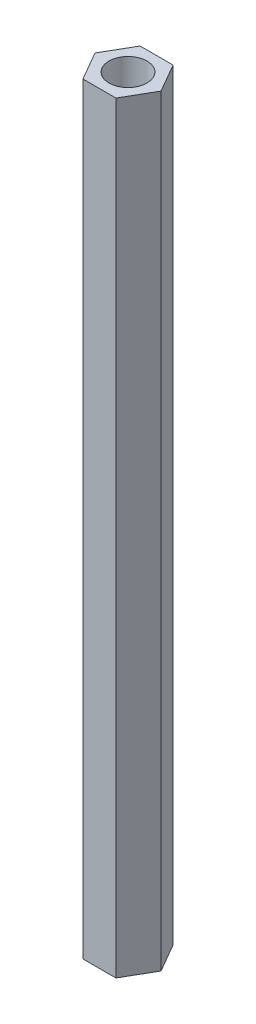
SolidWorks part; units mm, degrees
ref_plane "前视基准面" through (0, 0, 0) normal (0, 0, 1) x (1, 0, 0)
ref_plane "上视基准面" through (0, 0, 0) normal (0, 1, 0) x (1, 0, 0)
ref_plane "右视基准面" through (0, 0, 0) normal (1, 0, 0) x (0, 0, -1)
sketch "草图1" plane through (0, 0, 0) normal (0, 1, 0) x (1, 0, 0)
  line L1 (1.7321, 3) -> (-1.7321, 3)
  line L2 (-1.7321, 3) -> (-3.4641, 0)
  line L3 (-3.4641, 0) -> (-1.7321, -3)
  line L4 (-1.7321, -3) -> (1.7321, -3)
  line L5 (1.7321, -3) -> (3.4641, 0)
  line L6 (3.4641, 0) -> (1.7321, 3)
  circle A0 centre (0, 0) radius 3 construction
  circle A1 centre (0, 0) radius 2
  dimension "D1" = 6
  dimension "D2" = 4
extrude "凸台-拉伸1" add sketch "草图1" along normal blind 80
